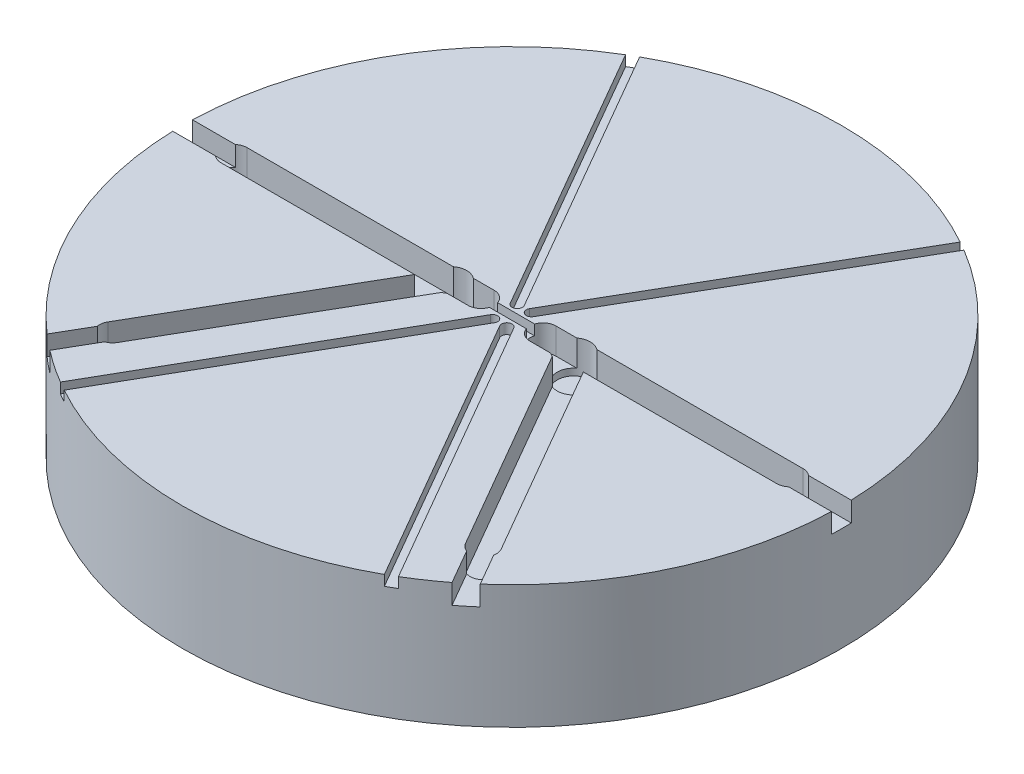
SolidWorks part; units mm, degrees
ref_plane "Front Plane" through (0, 0, 0) normal (0, 0, 1) x (1, 0, 0)
ref_plane "Top Plane" through (0, 0, 0) normal (0, 1, 0) x (1, 0, 0)
ref_plane "Right Plane" through (0, 0, 0) normal (1, 0, 0) x (0, 0, -1)
sketch "Sketch1" plane through (0, 0, 0) normal (0, 1, 0) x (1, 0, 0)
  circle A0 centre (0, 0) radius 8
extrude "Boss-Extrude1" add sketch "Sketch1" against normal blind 3
sketch "Sketch2" plane through (0, 0, 0) normal (0, 1, 0) x (1, 0, 0)
  line L0 (-0.75, 0) -> (0.75, 0) construction
  line L1 (-0.75, 0.1) -> (0.75, 0.1)
  line L2 (-0.75, -0.1) -> (0.75, -0.1)
  line L3 (0.1732, 0.3) -> (5, 8.66) construction
  line L4 (0.0649, 0.3625) -> (4.8917, 8.7225)
  line L5 (0.2815, 0.2375) -> (5.1083, 8.5975)
  line L6 (0.1732, -0.3) -> (5, -8.66) construction
  line L7 (0.2815, -0.2375) -> (5.1083, -8.5975)
  line L8 (0.0649, -0.3625) -> (4.8917, -8.7225)
  line L9 (-0.1732, -0.3) -> (-5, -8.7225) construction
  line L10 (-0.0647, -0.3622) -> (-4.8915, -8.7847)
  line L11 (-0.2817, -0.2378) -> (-5.1085, -8.6603)
  line L12 (-0.1732, 0.3) -> (-5, 8.66) construction
  line L13 (-0.2815, 0.2375) -> (-5.1083, 8.5975)
  line L14 (-0.0649, 0.3625) -> (-4.8917, 8.7225)
  arc A0 (-0.75, 0.1) -> (-0.75, -0.1) centre (-0.75, 0) ccw
  arc A1 (0.75, -0.1) -> (0.75, 0.1) centre (0.75, 0) ccw
  arc A2 (0.0649, 0.3625) -> (0.2815, 0.2375) centre (0.1732, 0.3) ccw
  arc A3 (5.1083, 8.5975) -> (4.8917, 8.7225) centre (5, 8.66) ccw
  arc A4 (0.2815, -0.2375) -> (0.0649, -0.3625) centre (0.1732, -0.3) ccw
  arc A5 (4.8917, -8.7225) -> (5.1083, -8.5975) centre (5, -8.66) ccw
  arc A6 (-0.0647, -0.3622) -> (-0.2817, -0.2378) centre (-0.1732, -0.3) ccw
  arc A7 (-5.1085, -8.6603) -> (-4.8915, -8.7847) centre (-5, -8.7225) ccw
  arc A8 (-0.2815, 0.2375) -> (-0.0649, 0.3625) centre (-0.1732, 0.3) ccw
  arc A9 (-4.8917, 8.7225) -> (-5.1083, 8.5975) centre (-5, 8.66) ccw
  point P2 (0, 0)
  point P8 (5, 8.66)
  point P9 (0.1732, 0.3)
  point P12 (2.5866, 4.48)
  point P17 (0.1732, -0.3)
  point P18 (5, -8.66)
  point P21 (2.5866, -4.48)
  point P26 (-0.1732, 0.3)
  point P27 (-0.1732, -0.3)
  point P28 (-5, 8.66)
  point P29 (-5, -8.7225)
  point P32 (-2.5866, -4.5113)
  point P37 (-2.5866, 4.48)
extrude "Cut-Extrude1" cut sketch "Sketch2" against normal blind 0.25
sketch "Sketch3" plane through (0, 0, 0) normal (0, 1, 0) x (1, 0, 0)
  circle A0 centre (1.5, 0) radius 0.4
  circle A1 centre (-1.5, 0) radius 0.4
extrude "Cut-Extrude2" cut sketch "Sketch3" against normal blind 0.8
sketch "Sketch4" plane through (0, 0, 0) normal (0, 1, 0) x (1, 0, 0)
  line L0 (-0.75, 0) -> (-6.75, 0) construction
  line L1 (-0.75, -0.3175) -> (-6.75, -0.3175)
  line L2 (-0.75, 0.3175) -> (-6.75, 0.3175)
  line L3 (0.75, 0) -> (6.75, 0) construction
  line L4 (0.75, 0.3175) -> (6.75, 0.3175)
  line L5 (0.75, -0.3175) -> (6.75, -0.3175)
  line L6 (-1.5, 0) -> (-4.5001, -5.1961) construction
  line L7 (-1.225, -0.1588) -> (-4.2251, -5.3549)
  line L8 (-1.775, 0.1588) -> (-4.775, -5.0374)
  line L9 (1.5, 0) -> (4.5001, -5.1961) construction
  line L10 (1.775, 0.1588) -> (4.775, -5.0374)
  line L11 (1.225, -0.1588) -> (4.2251, -5.3549)
  arc A0 (-0.75, -0.3175) -> (-0.75, 0.3175) centre (-0.75, 0) ccw
  arc A1 (-6.75, 0.3175) -> (-6.75, -0.3175) centre (-6.75, 0) ccw
  arc A2 (0.75, 0.3175) -> (0.75, -0.3175) centre (0.75, 0) ccw
  arc A3 (6.75, -0.3175) -> (6.75, 0.3175) centre (6.75, 0) ccw
  arc A4 (-1.225, -0.1588) -> (-1.775, 0.1588) centre (-1.5, 0) ccw
  arc A5 (-4.775, -5.0374) -> (-4.2251, -5.3549) centre (-4.5001, -5.1961) ccw
  arc A6 (1.775, 0.1588) -> (1.225, -0.1588) centre (1.5, 0) ccw
  arc A7 (4.2251, -5.3549) -> (4.775, -5.0374) centre (4.5001, -5.1961) ccw
  point P0 (-0.5, 0)
  point P2 (0.75, 0)
  point P8 (-3.75, 0)
  point P13 (3.75, 0)
  point P20 (-1.5, 0)
  point P21 (1.5, 0)
  point P22 (4.5001, -5.1961)
  point P23 (-4.5001, -5.1961)
  point P26 (-3, -2.5981)
  point P31 (3, -2.5981)
extrude "Cut-Extrude4" cut sketch "Sketch4" against normal blind 0.635 contours L2 A1 L1 A0 | L8 A5 L7 A4 | L5 A3 L4 A2 | L11 A7 L10 A6
sketch "Sketch5" plane through (0, 0, 0) normal (0, 1, 0) x (1, 0, 0)
  line L0 (-6.75, 0) -> (-8.75, 0) construction
  line L1 (-6.75, -0.24) -> (-8.75, -0.24)
  line L2 (-6.75, 0.24) -> (-8.75, 0.24)
  line L3 (6.75, 0) -> (8.75, 0) construction
  line L4 (6.75, 0.24) -> (8.75, 0.24)
  line L5 (6.75, -0.24) -> (8.75, -0.24)
  line L6 (-4.5001, -5.1961) -> (-7.052, -9.616) construction
  line L7 (-4.2922, -5.3161) -> (-6.8441, -9.736)
  line L8 (-4.7079, -5.0761) -> (-7.2598, -9.496)
  line L9 (4.5001, -5.1961) -> (6.9827, -9.496) construction
  line L10 (4.7079, -5.0761) -> (7.1905, -9.376)
  line L11 (4.2922, -5.3161) -> (6.7749, -9.616)
  arc A0 (-6.75, -0.24) -> (-6.75, 0.24) centre (-6.75, 0) ccw
  arc A1 (-8.75, 0.24) -> (-8.75, -0.24) centre (-8.75, 0) ccw
  arc A2 (6.75, 0.24) -> (6.75, -0.24) centre (6.75, 0) ccw
  arc A3 (8.75, -0.24) -> (8.75, 0.24) centre (8.75, 0) ccw
  arc A4 (-4.2922, -5.3161) -> (-4.7079, -5.0761) centre (-4.5001, -5.1961) ccw
  arc A5 (-7.2598, -9.496) -> (-6.8441, -9.736) centre (-7.052, -9.616) ccw
  arc A6 (4.7079, -5.0761) -> (4.2922, -5.3161) centre (4.5001, -5.1961) ccw
  arc A7 (6.7749, -9.616) -> (7.1905, -9.376) centre (6.9827, -9.496) ccw
  point P4 (-7.75, 0)
  point P12 (7.75, 0)
  point P19 (-5.776, -7.4061)
  point P26 (5.7414, -7.3461)
extrude "Cut-Extrude6" cut sketch "Sketch5" against normal blind 0.48
